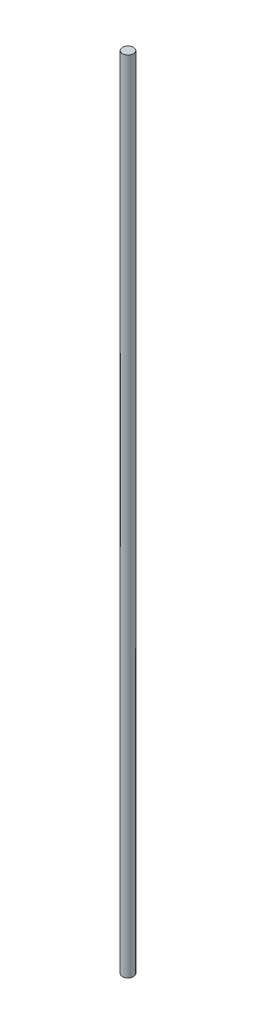
SolidWorks part; units mm, degrees
ref_plane "Alzado" through (0, 0, 0) normal (0, 0, 1) x (1, 0, 0)
ref_plane "Planta" through (0, 0, 0) normal (0, 1, 0) x (1, 0, 0)
ref_plane "Vista lateral" through (0, 0, 0) normal (1, 0, 0) x (0, 0, -1)
sketch "Croquis1" plane through (0, 0, 0) normal (0, 1, 0) x (1, 0, 0)
  circle A0 centre (0, 0) radius 6.35
  dimension "D1" = 12.7
sketch "Croquis2" plane through (0, 0, 0) normal (0, 0, 1) x (1, 0, 0)
  line L0 (0, 0) -> (0, 920)
  dimension "D1" = 920
sweep "Barrer1" add profiles "Croquis1" path "Croquis2"
